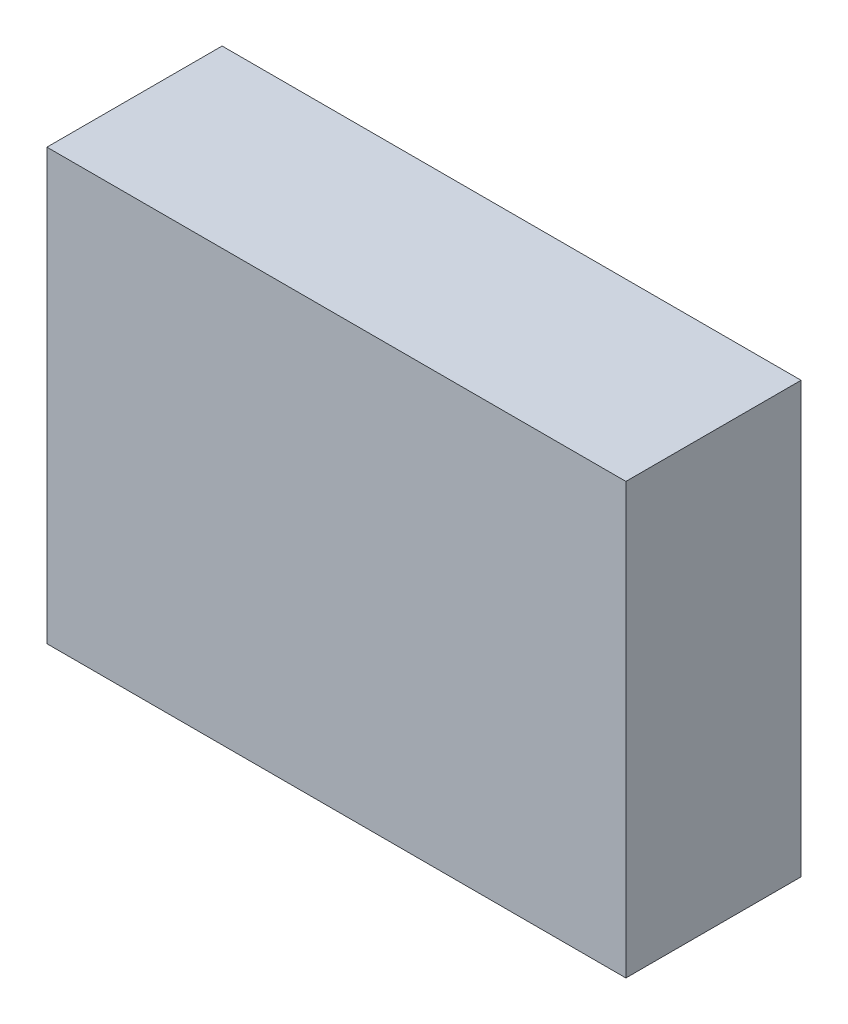
SolidWorks part; units mm, degrees
ref_plane "Plan de face" through (0, 0, 0) normal (0, 0, 1) x (1, 0, 0)
ref_plane "Plan de dessus" through (0, 0, 0) normal (0, 1, 0) x (1, 0, 0)
ref_plane "Plan de droite" through (0, 0, 0) normal (1, 0, 0) x (0, 0, -1)
sketch "Esquisse1" plane through (0, 0, 0) normal (0, 0, 1) x (1, 0, 0)
  line L1 (66.1, 49.1) -> (-66.1, 49.1)
  line L2 (66.1, 49.1) -> (66.1, -49.1)
  line L3 (66.1, -49.1) -> (-66.1, -49.1)
  line L4 (-66.1, 49.1) -> (-66.1, -49.1)
  line L5 (66.1, 49.1) -> (-66.1, -49.1) construction
  line L6 (66.1, -49.1) -> (-66.1, 49.1) construction
  point P0 (0, 0)
  dimension "D1" = 98.2
  dimension "D2" = 132.2
extrude "Boss.-Extru.1" add sketch "Esquisse1" along normal blind 40
